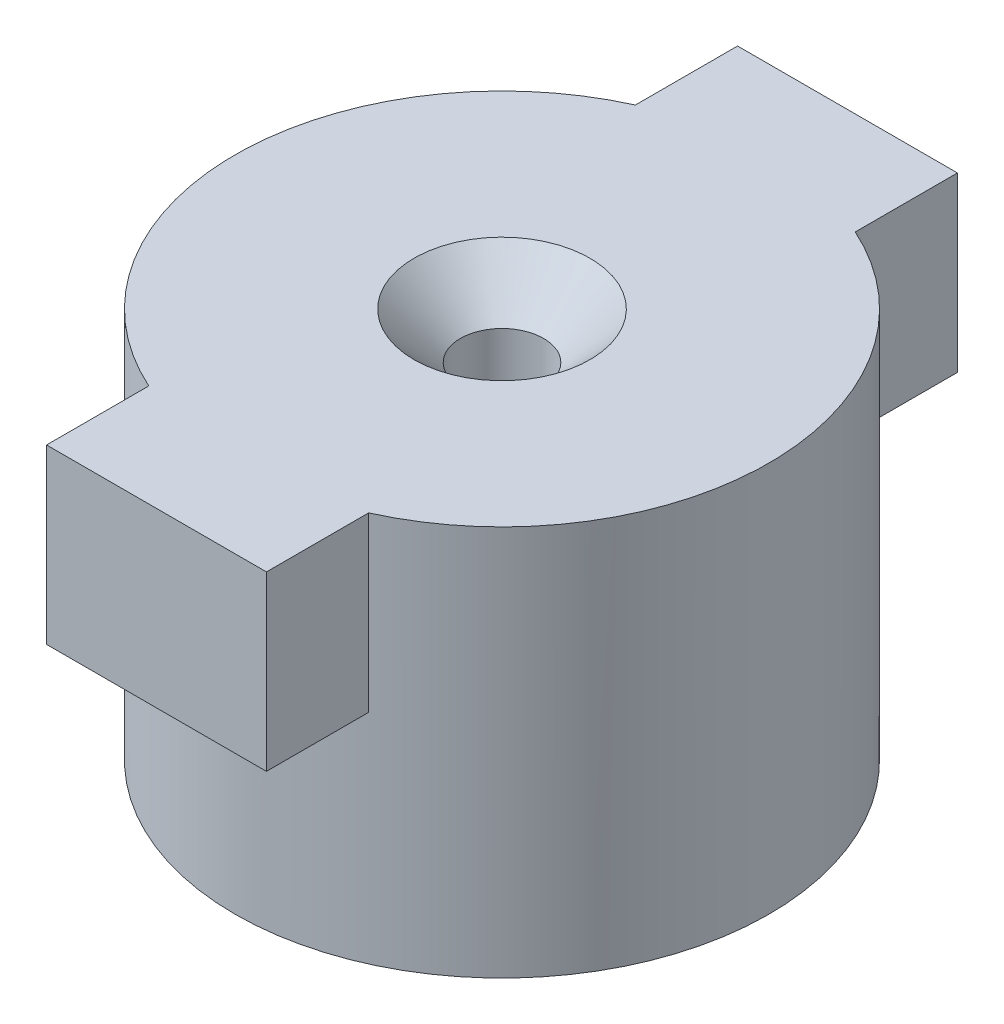
SolidWorks part; units mm, degrees
ref_plane "Front Plane" through (0, 0, 0) normal (0, 0, 1) x (1, 0, 0)
ref_plane "Top Plane" through (0, 0, 0) normal (0, 1, 0) x (1, 0, 0)
ref_plane "Right Plane" through (0, 0, 0) normal (1, 0, 0) x (0, 0, -1)
sketch "Sketch1" plane through (0, 0, 0) normal (0, 1, 0) x (1, 0, 0)
  circle A0 centre (0, 0) radius 17
  dimension "D1" = 34
extrude "Boss-Extrude1" add sketch "Sketch1" along normal blind 24.88
sketch "Sketch2" plane through (0, 24.88, 0) normal (0, 1, 0) x (1, 0, 0)
  line L1 (-7, 22) -> (7, 22)
  line L2 (-7, 22) -> (-7, -22)
  line L3 (-7, -22) -> (7, -22)
  line L4 (7, 22) -> (7, -22)
  point P4 (-7, 0)
  point P6 (17.1535, 22.5)
  point P7 (10.1234, 22.5)
  point P8 (0, 22)
  dimension "D1" = 44
  dimension "D2" = 14
extrude "Boss-Extrude2" add sketch "Sketch2" against normal blind 11
hole_wizard "CSK for M5 SFHCS1" positions "Sketch3" profile "Sketch4" countersink size "M5" standard "ANSI Metric" end condition through all
sketch "Sketch3" plane through (0, 24.88, 0) normal (0, 1, 0) x (1, 0, 0)
  point P0 (0, 0)
sketch "Sketch4" plane through (0, 24.88, 0) normal (1, 0, 0) x (0, 0, 1)
  line L0 (0, 0) -> (0, 24.88)
  line L1 (0, 24.88) -> (2.65, 24.88)
  line L2 (2.65, 24.88) -> (2.65, 2.95)
  line L3 (2.65, 2.95) -> (5.6, 0)
  line L5 (5.6, 0) -> (0, 0)
  line L6 (-2.65, 2.95) -> (-5.6, 0) construction
  line L11 (0, -6.35) -> (0, 107.95) construction
  dimension "Thru Hole Dia." = 5.3
  dimension "Thru Hole Depth" = 24.88
  dimension "Near C'Sink Dia." = 11.2
  dimension "Near C'Sink Angle" = 90
